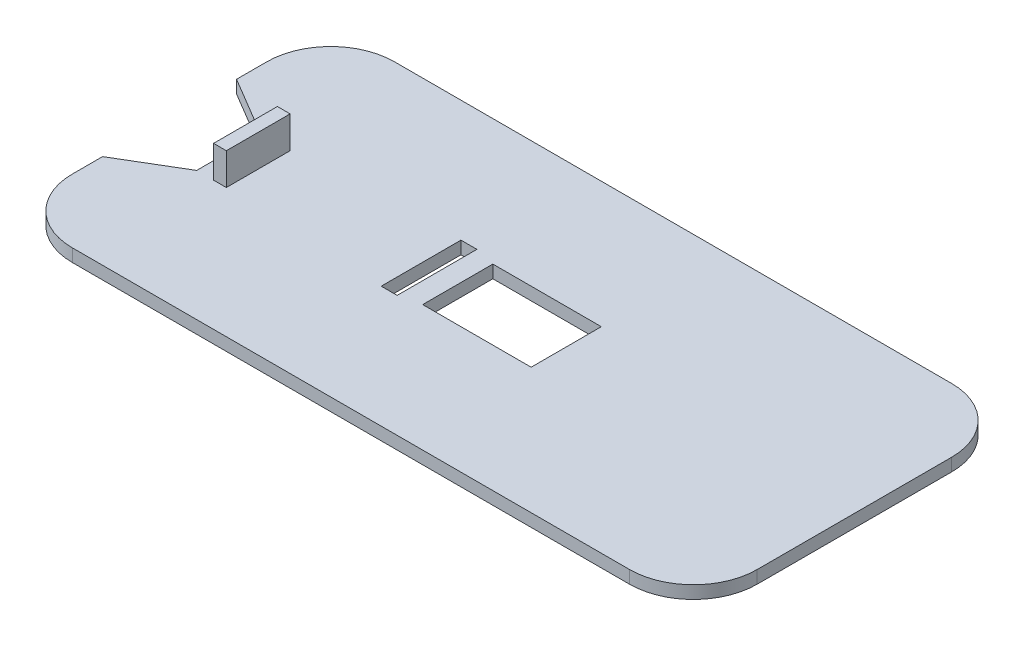
SolidWorks part; units mm, degrees
ref_plane "Front Plane" through (0, 0, 0) normal (0, 0, 1) x (1, 0, 0)
ref_plane "Top Plane" through (0, 0, 0) normal (0, 1, 0) x (1, 0, 0)
ref_plane "Right Plane" through (0, 0, 0) normal (1, 0, 0) x (0, 0, -1)
sketch "Sketch1" plane through (0, 0, 0) normal (0, 1, 0) x (1, 0, 0)
  line L0 (81.2702, 161.2523) -> (295.9702, 161.2523)
  line L1 (101.2702, 181.2523) -> (275.9702, 181.2523)
  line L2 (81.2702, 161.2523) -> (81.2702, 100.2523)
  line L3 (101.2702, 80.2523) -> (275.9702, 80.2523)
  line L4 (295.9702, 161.2523) -> (295.9702, 100.2523)
  line L5 (81.2702, 100.2523) -> (295.9702, 100.2523)
  line L6 (114.7702, 181.2523) -> (114.7702, 80.2523)
  line L7 (262.4702, 181.2523) -> (262.4702, 80.2523)
  line L8 (178.6202, 181.2523) -> (178.6202, 80.2523)
  line L9 (198.6202, 181.2523) -> (198.6202, 80.2523)
  line L10 (188.6202, 181.2523) -> (188.6202, 80.2523)
  line L11 (188.6202, 181.2523) -> (188.6202, 80.2523)
  arc A0 (81.2702, 100.2523) -> (101.2702, 80.2523) centre (101.2702, 100.2523) ccw
  arc A1 (101.2702, 181.2523) -> (81.2702, 161.2523) centre (101.2702, 161.2523) ccw
  arc A2 (275.9702, 80.2523) -> (295.9702, 100.2523) centre (275.9702, 100.2523) ccw
  arc A3 (275.9702, 181.2523) -> (295.9702, 161.2523) centre (275.9702, 161.2523) cw
  point P22 (81.2702, 80.2523)
  point P25 (81.2702, 181.2523)
  point P30 (295.9702, 181.2523)
  dimension "D11" = 20
  dimension "D12" = 20
  dimension "D1" = 20
  dimension "D2" = 20
  dimension "D3" = 61
  dimension "D4" = 33.5
  dimension "D5" = 33.5
  dimension "D6" = 63.85
  dimension "D7" = 63.85
  dimension "D8" = 0
  dimension "D9" = 10
  dimension "D10" = 10
  dimension "L_base" = 214.7
  dimension "W_base" = 101
extrude "Boss-Extrude7" add sketch "Sketch1" along normal blind 4 contours L6 L5 L2 L3 | L8 L5 L6 L3 | L10 L5 L8 L3 | L11 L5 L10 L3 | L5 L11 L3 L9 | L5 L9 L3 L7 | L5 L7 L3 L4 | L0 L7 L5 L4 | L0 L9 L5 L7 | L0 L11 L5 L9 | L11 L0 L10 L5 | L8 L0 L6 L5 | L6 L0 L2 L5 | L10 L0 L8 L5 | L6 L1 L2 L0 | L8 L1 L6 L0 | L10 L1 L8 L0 | L11 L1 L10 L0 | L1 L11 L0 L9 | L1 L9 L0 L7 | L1 L7 L0 L4
sketch "Sketch3" plane through (0, 4, 0) normal (0, 1, 0) x (1, 0, 0)
  line L0 (101.2702, 181.2523) -> (275.9702, 181.2523) construction
  line L1 (171.6202, 141.7523) -> (205.6202, 141.7523)
  line L2 (171.6202, 141.7523) -> (171.6202, 119.7523)
  line L3 (171.6202, 119.7523) -> (205.6202, 119.7523)
  line L4 (205.6202, 141.7523) -> (205.6202, 119.7523)
  line L5 (81.2702, 161.2523) -> (81.2702, 100.2523) construction
  dimension "W_TCS3200_Sensor" = 22
  dimension "L_TCS3200_Sensor" = 34
  dimension "D1" = 39.5
  dimension "D2" = 90.35
extrude "Cut-Extrude2" cut sketch "Sketch3" against normal blind 4 contours L4 L3 L2 L1
sketch "Sketch6" plane through (0, 4, 0) normal (0, 1, 0) x (1, 0, 0)
  line L0 (81.2702, 151.7523) -> (81.2702, 109.7523)
  line L1 (81.2702, 161.2523) -> (81.2702, 100.2523) construction
  line L2 (81.2702, 109.7523) -> (99.7702, 120.7523)
  line L3 (99.7702, 120.7523) -> (99.7702, 140.7523)
  line L4 (99.7702, 140.7523) -> (81.2702, 151.7523)
  line L5 (101.2702, 181.2523) -> (275.9702, 181.2523) construction
  dimension "D2" = 20
  dimension "D1" = 42
  dimension "D3" = 18.5
  dimension "D4" = 59.265
  dimension "D5" = 29.5
extrude "Cut-Extrude3" cut sketch "Sketch6" against normal blind 4
sketch "Sketch7" plane through (0, 4, 0) normal (0, 1, 0) x (1, 0, 0)
  line L0 (99.7702, 120.7523) -> (99.7702, 140.7523) construction
  line L1 (105.0702, 140.7523) -> (109.0702, 140.7523)
  line L2 (105.0702, 140.7523) -> (105.0702, 120.7523)
  line L3 (105.0702, 120.7523) -> (109.0702, 120.7523)
  line L4 (109.0702, 140.7523) -> (109.0702, 120.7523)
  line L5 (105.0702, 140.7523) -> (109.0702, 120.7523) construction
  line L6 (105.0702, 120.7523) -> (109.0702, 140.7523) construction
  line L7 (101.2702, 181.2523) -> (275.9702, 181.2523) construction
  point P0 (107.0702, 130.7523)
  point P7 (107.0702, 140.7523)
  dimension "D2" = 20
  dimension "D1" = 5.3
  dimension "D3" = 40.5
  dimension "D4" = 4
extrude "Boss-Extrude9" add sketch "Sketch7" against normal blind 14 and the other way blind 10
sketch "Sketch9" plane through (0, 0, 0) normal (0, -1, 0) x (-1, 0, 0)
  line L1 (-160.1202, 118.2523) -> (-165.1202, 118.2523)
  line L2 (-160.1202, 118.2523) -> (-160.1202, 143.2523)
  line L3 (-160.1202, 143.2523) -> (-165.1202, 143.2523)
  line L4 (-165.1202, 118.2523) -> (-165.1202, 143.2523)
  line L5 (-160.1202, 118.2523) -> (-165.1202, 143.2523) construction
  line L6 (-160.1202, 143.2523) -> (-165.1202, 118.2523) construction
  line L7 (-101.2702, 80.2523) -> (-275.9702, 80.2523) construction
  line L8 (-171.6202, 141.7523) -> (-171.6202, 119.7523) construction
  point P0 (-162.6202, 130.7523)
  dimension "D1" = 25
  dimension "D2" = 5
  dimension "D4" = 38
  dimension "D3" = 6.5
extrude "Cut-Extrude4" cut sketch "Sketch9" against normal blind 4
sketch "Sketch10" plane through (0, 4, 0) normal (0, 1, 0) x (1, 0, 0)
  line L0 (205.6202, 141.7523) -> (205.6202, 119.7523) construction
  line L1 (209.6202, 152.2523) -> (252.6202, 152.2523)
  line L2 (209.6202, 152.2523) -> (209.6202, 109.2523)
  line L3 (209.6202, 109.2523) -> (252.6202, 109.2523)
  line L4 (252.6202, 152.2523) -> (252.6202, 109.2523)
  line L5 (209.6202, 152.2523) -> (252.6202, 109.2523) construction
  line L6 (209.6202, 109.2523) -> (252.6202, 152.2523) construction
  line L7 (101.2702, 181.2523) -> (275.9702, 181.2523) construction
  line L8 (101.2702, 181.2523) -> (275.9702, 181.2523) construction
  line L13 (81.2702, 161.2523) -> (81.2702, 151.7523) construction
  line L14 (101.2702, 80.2523) -> (275.9702, 80.2523) construction
  line L15 (295.9702, 161.2523) -> (295.9702, 100.2523) construction
  circle A0 centre (96.2702, 166.2523) radius 5
  circle A1 centre (280.9702, 166.2523) radius 5
  circle A2 centre (280.9702, 95.2523) radius 5
  circle A3 centre (96.2702, 95.2523) radius 5
  point P0 (231.1202, 130.7523)
  dimension "D4" = 10
  dimension "D1" = 43
  dimension "D2" = 4
  dimension "D3" = 29
  dimension "D5" = 15
  dimension "D6" = 15
  dimension "D9" = 15
  dimension "D10" = 15
  dimension "D7" = 2
  dimension "D8" = 2
equation "\"D2@Sketch1\"=\"D1@Sketch1\""
equation "\"D5@Sketch1\"=\"D4@Sketch1\""
equation "\"D7@Sketch1\"=\"D6@Sketch1\""
equation "\"D10@Sketch1\"=\"D9@Sketch1\""
equation "\"D1@Sketch3\"=\"W_base@Sketch1\"/2-\"W_TCS3200_Sensor@Sketch3\"/2"
equation "\"D2@Sketch3\"=\"L_base@Sketch1\"/2-\"L_TCS3200_Sensor@Sketch3\"/2"
equation "\"D5@Sketch6\"=(\"W_base@Sketch1\"-\"D1@Sketch6\")/2"
equation "\"D4@Sketch6\"=atn( \"D3@Sketch6\"/((\"D1@Sketch6\"-\"D2@Sketch6\")/2))"
equation "\"D2@Sketch7\"=\"D2@Sketch6\""
equation "\"D3@Sketch7\"=(\"W_base@Sketch1\"-\"D2@Sketch7\")/2"
equation "\"D4@Sketch9\"=(\"W_base@Sketch1\"-\"D1@Sketch9\")/2"
equation "\"D3@Sketch10\"=(\"W_base@Sketch1\"-\"D1@Sketch10\")/2"
equation "\"D9@Sketch10\"=\"D5@Sketch10\""
equation "\"D10@Sketch10\"=\"D6@Sketch10\""
